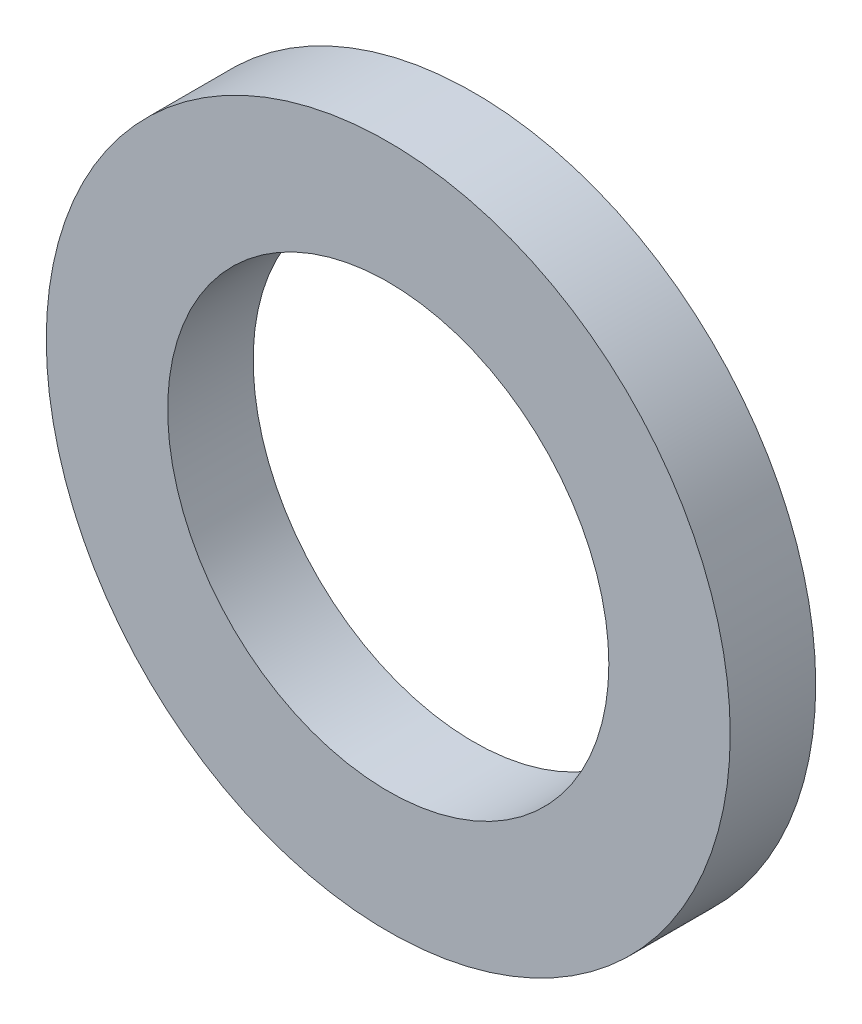
SolidWorks part; units mm, degrees
material "SS 304 (Default)"
ref_plane "Front Plane" through (0, 0, 0) normal (0, 0, 1) x (1, 0, 0)
ref_plane "Top Plane" through (0, 0, 0) normal (0, 1, 0) x (1, 0, 0)
ref_plane "Right Plane" through (0, 0, 0) normal (1, 0, 0) x (0, 0, -1)
sketch "Sketch1" plane through (0, 0, 0) normal (0, 0, 1) x (1, 0, 0)
  circle A0 centre (0, 0) radius 6.35
  circle A1 centre (0, 0) radius 4.0957
  dimension "D1" = 8.1915
  dimension "Diameter" = 12.7
extrude "Extrude1" add sketch "Sketch1" along normal mid plane 1.5875
